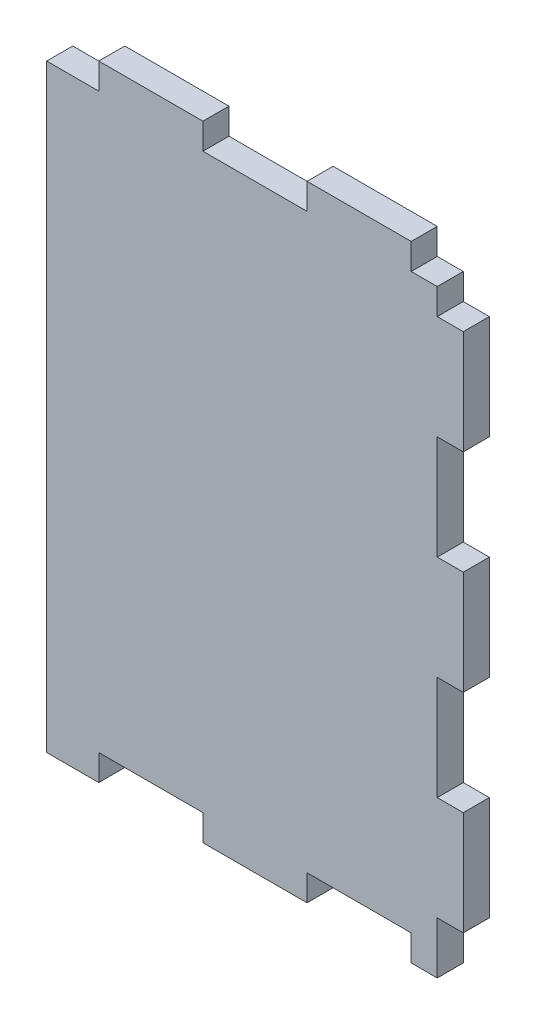
SolidWorks part; units mm, degrees
ref_plane "Front Plane" through (0, 0, 0) normal (0, 0, 1) x (1, 0, 0)
ref_plane "Top Plane" through (0, 0, 0) normal (0, 1, 0) x (1, 0, 0)
ref_plane "Right Plane" through (0, 0, 0) normal (1, 0, 0) x (0, 0, -1)
sketch "Sketch1" plane through (0, 0, 0) normal (0, 0, 1) x (1, 0, 0)
  line L1 (0, 0) -> (50.8, 0)
  line L2 (0, 0) -> (0, 76.2)
  line L3 (0, 76.2) -> (50.8, 76.2)
  line L4 (50.8, 0) -> (50.8, 76.2)
  dimension "D1" = 76.2
  dimension "D2" = 50.8
extrude "Extrude1" add sketch "Sketch1" along normal blind 3.175
sketch "Sketch3" plane through (0, 0, 3.175) normal (0, 0, 1) x (1, 0, 0)
  line L0 (50.8, 0) -> (50.8, 76.2) construction
  line L1 (50.8, 69.85) -> (47.625, 69.85)
  line L2 (50.8, 69.85) -> (50.8, 76.2)
  line L3 (50.8, 76.2) -> (47.625, 76.2)
  line L4 (47.625, 69.85) -> (47.625, 76.2)
  dimension "D1" = 6.35
  dimension "D2" = 3.175
  dimension "D3" = 6.35
extrude "Cut-Extrude1" cut sketch "Sketch3" against normal blind 3.175
pattern_linear "LPattern1" count 2 spacing 69.85 along (0, -1, 0) of "Cut-Extrude1"
sketch "Sketch4" plane through (0, 0, 3.175) normal (0, 0, 1) x (1, 0, 0)
  line L0 (50.8, 6.35) -> (50.8, 69.85) construction
  line L1 (50.8, 57.15) -> (47.625, 57.15)
  line L2 (50.8, 57.15) -> (50.8, 44.45)
  line L3 (50.8, 44.45) -> (47.625, 44.45)
  line L4 (47.625, 57.15) -> (47.625, 44.45)
  line L5 (47.625, 76.2) -> (0, 76.2) construction
  dimension "D1" = 12.7
  dimension "D2" = 3.175
  dimension "D3" = 19.05
extrude "Cut-Extrude2" cut sketch "Sketch4" against normal blind 3.175
pattern_linear "LPattern2" count 5 spacing 25.4 along (0, -1, 0) of "Cut-Extrude2"
sketch "Sketch5" plane through (0, 0, 3.175) normal (0, 0, 1) x (1, 0, 0)
  line L0 (0, 0) -> (47.625, 0) construction
  line L1 (19.05, 0) -> (6.35, 0)
  line L2 (19.05, 0) -> (19.05, 3.175)
  line L3 (19.05, 3.175) -> (6.35, 3.175)
  line L4 (6.35, 0) -> (6.35, 3.175)
  dimension "D1" = 6.35
  dimension "D2" = 12.7
  dimension "D3" = 3.175
extrude "Cut-Extrude3" cut sketch "Sketch5" against normal blind 3.175
sketch "Sketch6" plane through (0, 0, 3.175) normal (0, 0, 1) x (1, 0, 0)
  line L1 (0, 76.2) -> (6.35, 76.2)
  line L2 (0, 76.2) -> (0, 73.025)
  line L3 (0, 73.025) -> (6.35, 73.025)
  line L4 (6.35, 76.2) -> (6.35, 73.025)
  dimension "D1" = 6.35
  dimension "D2" = 3.175
extrude "Cut-Extrude4" cut sketch "Sketch6" against normal blind 3.175
pattern_linear "LPattern3" count 2 spacing 44.45 along (1, 0, 0) of "Cut-Extrude4"
pattern_linear "LPattern4" count 2 spacing 25.4 along (1, 0, 0) of "Cut-Extrude3"
sketch "Sketch7" plane through (0, 0, 3.175) normal (0, 0, 1) x (1, 0, 0)
  line L0 (44.45, 76.2) -> (6.35, 76.2) construction
  line L1 (19.05, 76.2) -> (31.75, 76.2)
  line L2 (19.05, 76.2) -> (19.05, 73.025)
  line L3 (19.05, 73.025) -> (31.75, 73.025)
  line L4 (31.75, 76.2) -> (31.75, 73.025)
  line L5 (0, 73.025) -> (0, 0) construction
  dimension "D1" = 3.175
  dimension "D2" = 12.7
  dimension "D3" = 19.05
extrude "Cut-Extrude5" cut sketch "Sketch7" against normal through all
